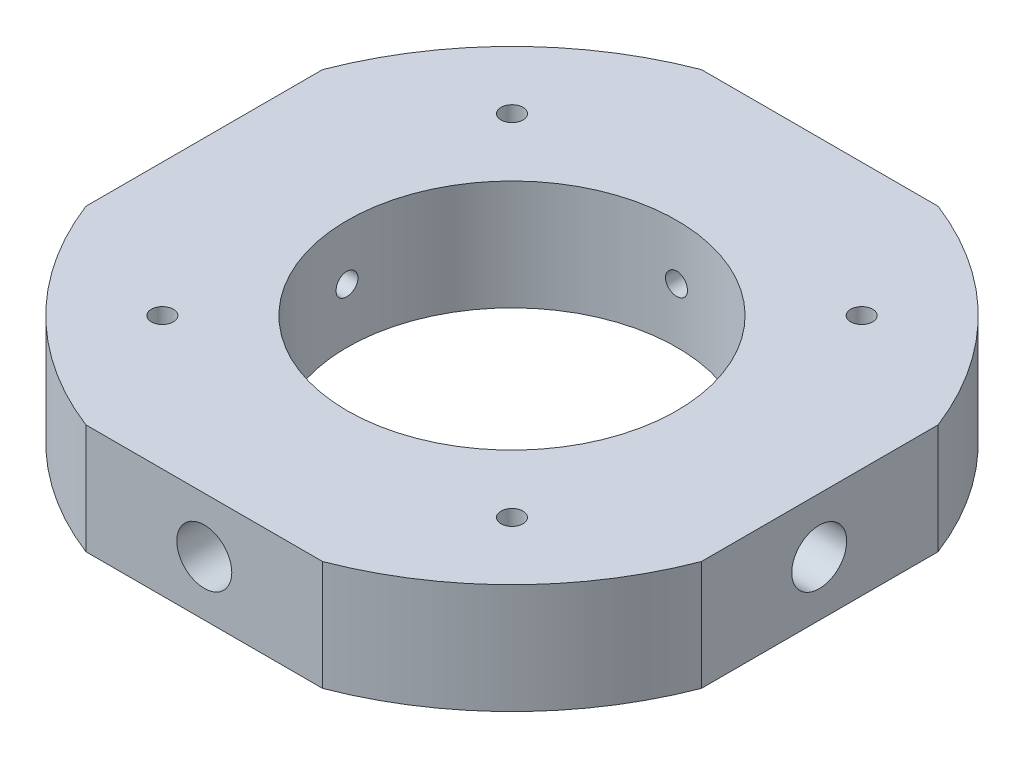
SolidWorks part; units mm, degrees
ref_plane "Front Plane" through (0, 0, 0) normal (0, 0, 1) x (1, 0, 0)
ref_plane "Top Plane" through (0, 0, 0) normal (0, 1, 0) x (1, 0, 0)
ref_plane "Right Plane" through (0, 0, 0) normal (1, 0, 0) x (0, 0, -1)
sketch "Sketch1" plane through (0, 0, 0) normal (0, 1, 0) x (1, 0, 0)
  circle A0 centre (0, 0) radius 15
  circle A1 centre (0, 0) radius 30
  dimension "D1" = 30
  dimension "D2" = 15
extrude "Boss-Extrude1" add sketch "Sketch1" along normal blind 10
sketch "Sketch2" plane through (0, 10, 0) normal (0, 1, 0) x (1, 0, 0)
  line L1 (-10.7703, 28) -> (10.7703, 28)
  line L2 (-10.7703, 28) -> (-10.7703, -28)
  line L3 (-10.7703, -28) -> (10.7703, -28)
  line L4 (10.7703, 28) -> (10.7703, -28)
  line L5 (0, -28) -> (0, 28) construction
  line L6 (-10.7703, 0) -> (10.7703, 0) construction
  line L7 (-28, 10.7703) -> (28, 10.7703)
  line L8 (-28, 10.7703) -> (-28, -10.7703)
  line L9 (-28, -10.7703) -> (28, -10.7703)
  line L10 (28, 10.7703) -> (28, -10.7703)
  line L11 (0, -10.7703) -> (0, 10.7703) construction
  line L12 (-28, 0) -> (28, 0) construction
  circle A1 centre (0, 0) radius 30
  circle A2 centre (0, 0) radius 30
  point P6 (0, -30)
  point P10 (30, 0)
  circle M6 centre (0, 0) radius 30
  dimension "D2" = 2
  dimension "D3" = 2
  dimension "D1" = 0
extrude "Cut-Extrude1" cut sketch "Sketch2" against normal blind 43 contours L1 M6 | L8 M6 | L10 M6 | L3 M6
sketch "Sketch4" plane through (0, 10, 0) normal (0, 1, 0) x (1, 0, 0)
  line L0 (-21.2132, 21.2132) -> (-10.6066, 10.6066) construction
  line L1 (21.2132, 21.2132) -> (10.6066, 10.6066) construction
  line L2 (-21.2132, -21.2132) -> (-10.6066, -10.6066) construction
  line L3 (21.2132, -21.2132) -> (10.6066, -10.6066) construction
  line L4 (10.7703, 28) -> (-10.7703, 28)
  line L5 (-28, 10.7703) -> (-28, -10.7703)
  line L6 (-10.7703, -28) -> (10.7703, -28)
  line L7 (28, -10.7703) -> (28, 10.7703)
  line L9 (-28, 10.7703) -> (-28, -10.7703)
  line L11 (28, -10.7703) -> (28, 10.7703)
  circle A0 centre (0, 0) radius 15 construction
  circle A1 centre (-15.9099, 15.9099) radius 1
  circle A2 centre (15.9099, 15.9099) radius 1
  circle A3 centre (15.9099, -15.9099) radius 1
  arc A4 (-10.7703, 28) -> (-28, 10.7703) centre (0, 0) ccw
  arc A5 (-28, -10.7703) -> (-10.7703, -28) centre (0, 0) ccw
  arc A6 (10.7703, -28) -> (28, -10.7703) centre (0, 0) ccw
  arc A7 (28, 10.7703) -> (10.7703, 28) centre (0, 0) ccw
  arc A8 (-10.7703, 28) -> (-28, 10.7703) centre (0, 0) ccw
  arc A9 (-28, -10.7703) -> (-10.7703, -28) centre (0, 0) ccw
  arc A10 (10.7703, -28) -> (28, -10.7703) centre (0, 0) ccw
  arc A11 (28, 10.7703) -> (10.7703, 28) centre (0, 0) ccw
  circle A12 centre (-15.9099, -15.9099) radius 1
  dimension "D2" = 2
  dimension "D3" = 2
  dimension "D4" = 2
  dimension "D5" = 2
  dimension "D1" = 0
extrude "Cut-Extrude3" cut sketch "Sketch4" against normal blind 43 contours A3 | A12 | A1 | A2
sketch "Sketch5" plane through (0, 0, -28) normal (0, 0, -1) x (-1, 0, 0)
  line L0 (0, 10) -> (0, 0) construction
  line L4 (10.7703, 0) -> (10.7703, 10)
  line L5 (10.7703, 10) -> (-10.7703, 10)
  line L6 (-10.7703, 10) -> (-10.7703, 0)
  line L7 (-10.7703, 0) -> (10.7703, 0)
  line L10 (-10.7703, 10) -> (-10.7703, 0)
  line L11 (0, 0) -> (10.7703, 0)
  circle A0 centre (0, 5) radius 1
  dimension "D2" = 2
  dimension "D1" = 0
extrude "Cut-Extrude4" cut sketch "Sketch5" against normal blind 70 contours L0 A0 | A0 L0
sketch "Sketch6" plane through (28, 0, 0) normal (1, 0, 0) x (0, 0, -1)
  line L0 (-10.7703, 10) -> (-10.7703, 0)
  line L1 (-0.0916, 10) -> (10.5872, 10)
  line L2 (0, 0) -> (10.5872, 0)
  line L3 (10.5872, 10) -> (10.5872, 0)
  line L4 (-0.0916, 10) -> (0, 0) construction
  circle A0 centre (-0.0458, 5) radius 1
  dimension "D1" = 2
extrude "Cut-Extrude5" cut sketch "Sketch6" against normal blind 70 contours A0 L4 | L4 A0
sketch "Sketch8" plane through (0, 0, -28) normal (0, 0, -1) x (-1, 0, 0)
  circle A0 centre (0, 5) radius 2.5
  dimension "D1" = 5
extrude "Cut-Extrude6" cut sketch "Sketch8" against normal blind 4
sketch "Sketch9" plane through (28, 0, 0) normal (1, 0, 0) x (0, 0, -1)
  circle A0 centre (-0.0458, 5) radius 1 construction
  circle A1 centre (-0.0458, 5) radius 1
  circle A2 centre (-0.0458, 5) radius 2.5
  dimension "D1" = 5
extrude "Cut-Extrude7" cut sketch "Sketch9" against normal blind 4
sketch "Sketch10" plane through (0, 0, 28) normal (0, 0, 1) x (1, 0, 0)
  circle A0 centre (0, 5) radius 2.5
  dimension "D1" = 5
extrude "Cut-Extrude8" cut sketch "Sketch10" against normal blind 4
sketch "Sketch11" plane through (-28, 0, 0) normal (-1, 0, 0) x (0, 0, 1)
  circle A1 centre (0.0458, 5) radius 2.5
  dimension "D1" = 5
extrude "Cut-Extrude9" cut sketch "Sketch11" against normal blind 4
